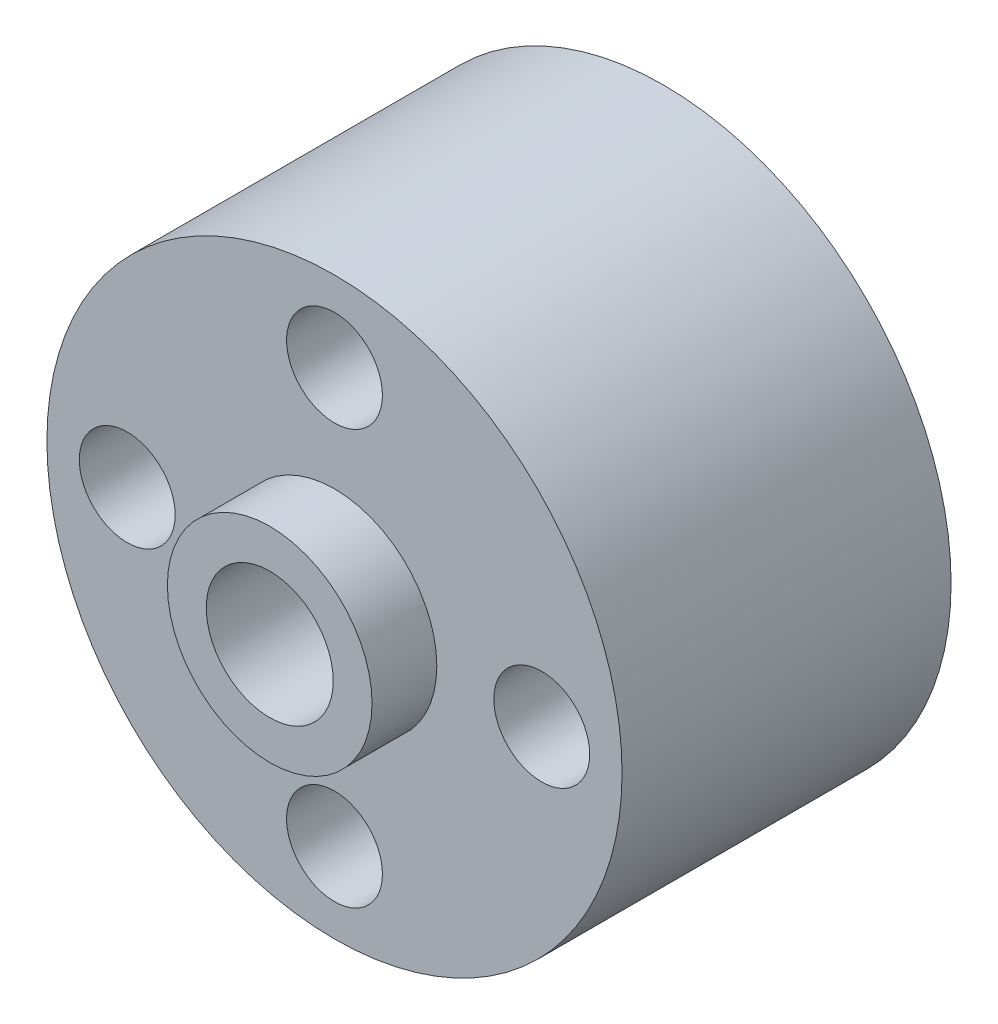
SolidWorks part; units mm, degrees
material "6061 Alloy"
ref_plane "Front Plane" through (0, 0, 0) normal (0, 0, 1) x (1, 0, 0)
ref_plane "Top Plane" through (0, 0, 0) normal (0, 1, 0) x (1, 0, 0)
ref_plane "Right Plane" through (0, 0, 0) normal (1, 0, 0) x (0, 0, -1)
sketch "Sketch1" plane through (0, 0, 0) normal (0, 0, 1) x (1, 0, 0)
  circle A0 centre (0, 0) radius 11.1
  dimension "D1" = 22.2
extrude "Extrude1" add sketch "Sketch1" against normal blind 12.7
sketch "Sketch3" plane through (0, 0, 0) normal (0, 0, 1) x (1, 0, 0)
  line L0 (0, 0) -> (0, 8) construction
  line L1 (0, 0) -> (-8, 0) construction
  line L2 (0, 0) -> (0, -8) construction
  line L3 (0, 0) -> (8, 0) construction
  circle A0 centre (0, 0) radius 8 construction
  circle A1 centre (8, 0) radius 1.85
  circle A2 centre (-8, 0) radius 1.85
  circle A3 centre (0, -8) radius 1.85
  circle A4 centre (0, 8) radius 1.85
  dimension "D1" = 16
  dimension "D2" = 3.7
extrude "Cut-Extrude1" cut sketch "Sketch3" against normal through all
sketch "Sketch6" plane through (0, 0, 0) normal (0, 0, 1) x (1, 0, 0)
  circle A0 centre (0, 0) radius 3.95
  dimension "D1" = 7.9
extrude "Extrude3" add sketch "Sketch6" along normal blind 2.5
sketch "Sketch7" plane through (0, 0, -12.7) normal (0, 0, -1) x (-1, 0, 0)
  circle A0 centre (0, 0) radius 3.95
  dimension "D1" = 7.9
extrude "Extrude4" add sketch "Sketch7" along normal blind 2.5
sketch "Sketch8" plane through (0, 0, 2.5) normal (0, 0, 1) x (1, 0, 0)
  circle A0 centre (0, 0) radius 2.45
  dimension "D1" = 4.9
extrude "Cut-Extrude2" cut sketch "Sketch8" against normal through all
